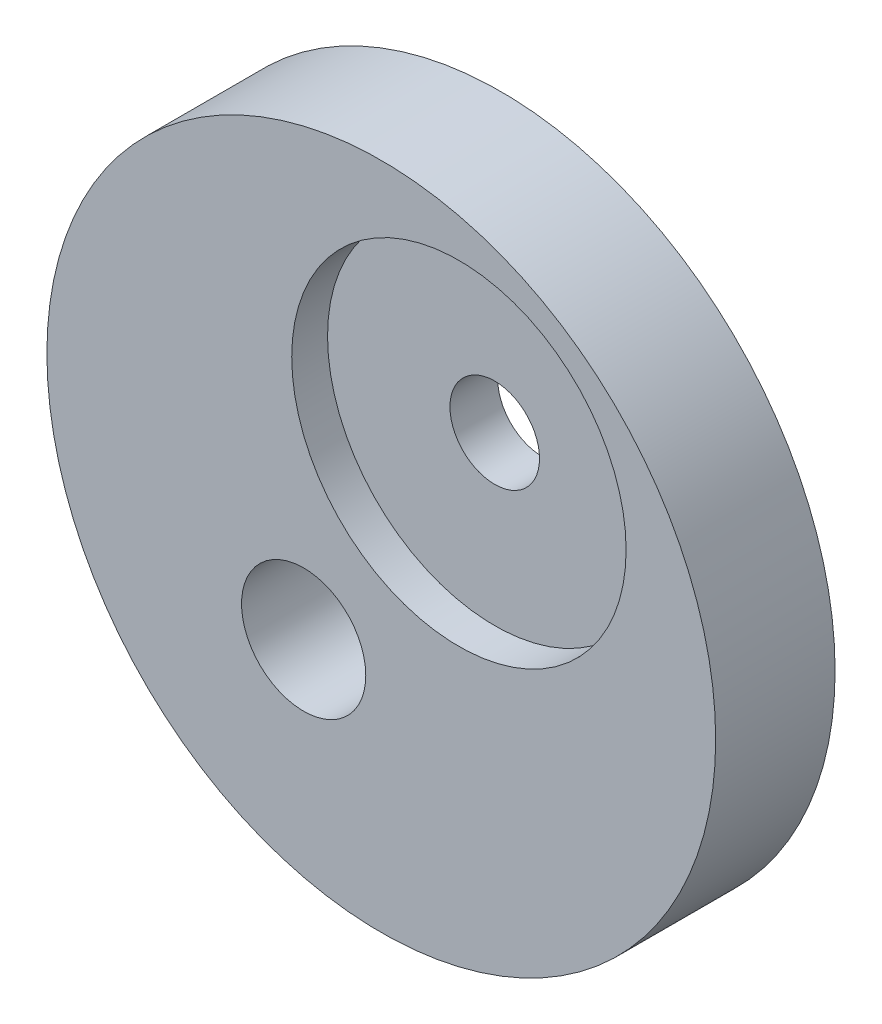
SolidWorks part; units mm, degrees
ref_plane "Plan de face" through (0, 0, 0) normal (0, 0, 1) x (1, 0, 0)
ref_plane "Plan de dessus" through (0, 0, 0) normal (0, 1, 0) x (1, 0, 0)
ref_plane "Plan de droite" through (0, 0, 0) normal (1, 0, 0) x (0, 0, -1)
sketch "Esquisse1" plane through (0, 0, 0) normal (0, 0, 1) x (1, 0, 0)
  line L0 (0, 0) -> (0, 3.2832) construction
  line L1 (-6.5, -10) -> (0, 0) construction
  line L2 (-6.5, -10) -> (0, -10) construction
  line L8 (-12.959, -14.4456) -> (6.459, 4.4456) construction
  line L9 (-12.959, 4.4456) -> (6.459, -14.4456) construction
  circle A0 centre (0, 0) radius 1.8746
  circle A1 centre (-6.5, -10) radius 2.6
  circle A2 centre (-3.25, -5) radius 14
  point P5 (-3.25, -5)
  point P25 (0, -4.0414)
  dimension "D1" = 6.5
  dimension "D2" = 10
extrude "Boss.-Extru.1" add sketch "Esquisse1" along normal blind 5
sketch "Esquisse2" plane through (0, 0, 5) normal (0, 0, 1) x (1, 0, 0)
  circle A0 centre (0, 0) radius 7
extrude "Enlèv. mat.-Extru.1" cut sketch "Esquisse2" against normal blind 1.5
sketch "Esquisse3" plane through (0, 0, 0) normal (0, 0, -1) x (-1, 0, 0)
  circle A0 centre (0, 0) radius 7
extrude "Enlèv. mat.-Extru.2" cut sketch "Esquisse3" against normal blind 1.5
